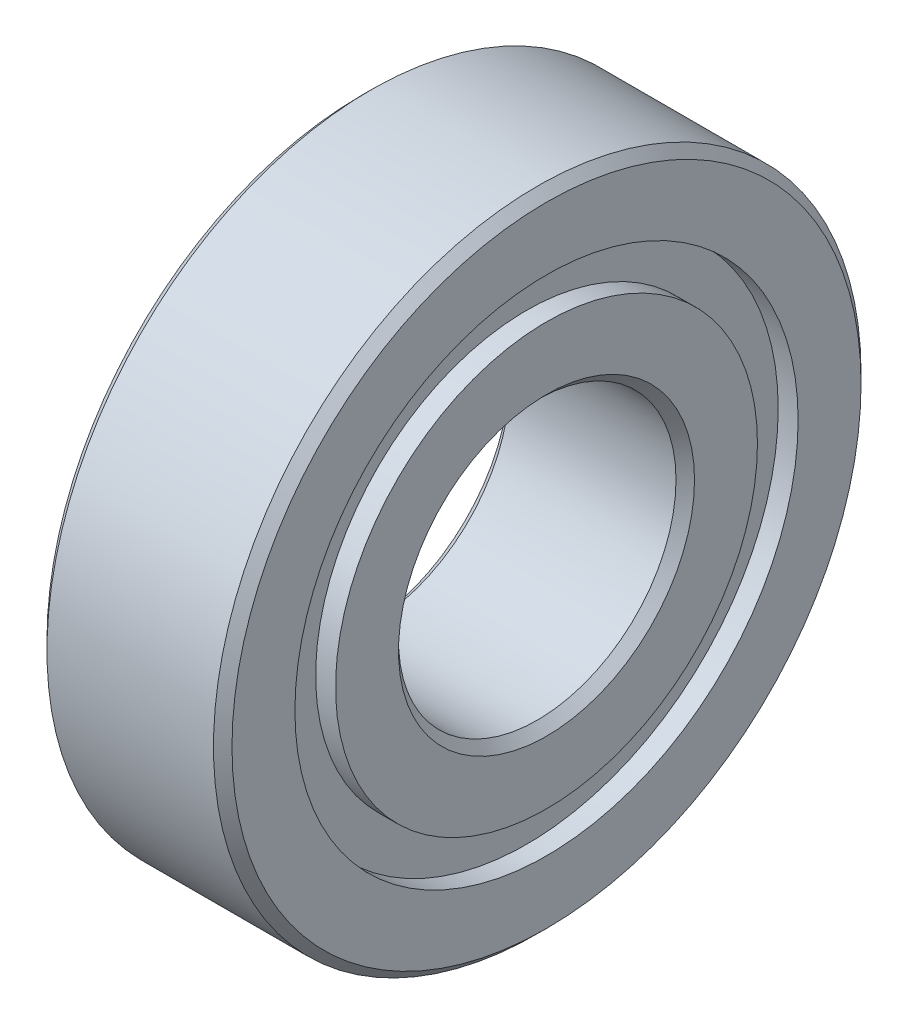
SolidWorks part; units mm, degrees
material "A8 (58-60 RC)"
ref_plane "Front" through (0, 0, 0) normal (0, 0, 1) x (1, 0, 0)
ref_plane "Top" through (0, 0, 0) normal (0, 1, 0) x (1, 0, 0)
ref_plane "Right" through (0, 0, 0) normal (1, 0, 0) x (0, 0, -1)
sketch "Sketch1" plane through (0, 0, 0) normal (0, 0, 1) x (1, 0, 0)
  line L0 (4, 13.6) -> (3.6, 14)
  line L1 (3.6, 14) -> (-3.6, 14)
  line L2 (-3.6, 14) -> (-4, 13.6)
  line L3 (-4, 13.6) -> (-4, 10.8791)
  line L4 (-4, 10.8791) -> (-3.1389, 10.8791)
  line L5 (-3.1389, 10.8791) -> (-3.1389, 9.1209)
  line L6 (-3.1389, 9.1209) -> (-4, 9.1209)
  line L7 (-4, 9.1209) -> (-4, 6.4)
  line L8 (-4, 6.4) -> (-3.6, 6)
  line L9 (-3.6, 6) -> (3.6, 6)
  line L10 (3.6, 6) -> (4, 6.4)
  line L11 (4, 6.4) -> (4, 9.1209)
  line L12 (4, 9.1209) -> (3.1389, 9.1209)
  line L13 (3.1389, 9.1209) -> (3.1389, 10.8791)
  line L14 (3.1389, 10.8791) -> (4, 10.8791)
  line L15 (4, 10.8791) -> (4, 13.6)
  line L16 (-4, 0) -> (4, 0) construction
revolve "Revolve1" add sketch "Sketch1" angle 360 about L16
